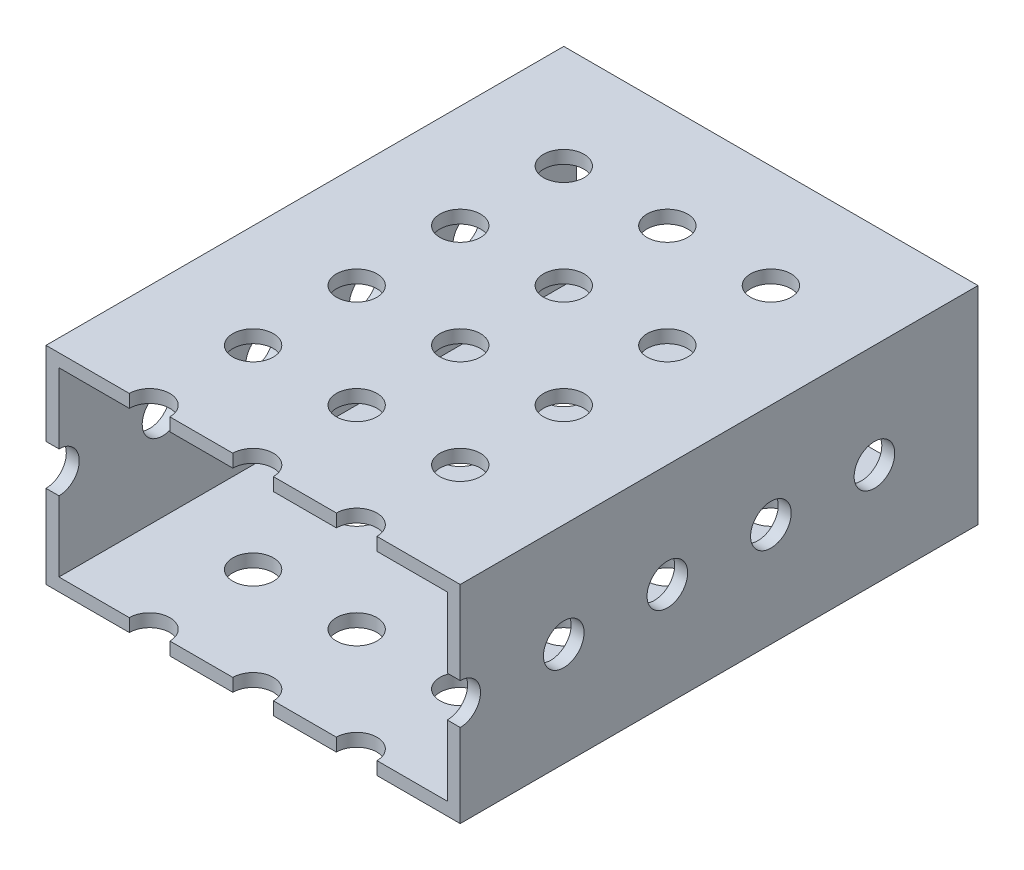
SolidWorks part; units mm, degrees
ref_plane "Front Plane" through (0, 0, 0) normal (0, 0, 1) x (1, 0, 0)
ref_plane "Top Plane" through (0, 0, 0) normal (0, 1, 0) x (1, 0, 0)
ref_plane "Right Plane" through (0, 0, 0) normal (1, 0, 0) x (0, 0, -1)
sketch "Sketch1" plane through (0, 0, 0) normal (0, 0, 1) x (1, 0, 0)
  line L0 (1.5875, 1.5875) -> (49.2125, 1.5875)
  line L1 (0, 0) -> (50.8, 0)
  line L2 (0, 0) -> (0, 25.4)
  line L3 (0, 25.4) -> (50.8, 25.4)
  line L4 (50.8, 0) -> (50.8, 25.4)
  line L5 (49.2125, 1.5875) -> (49.2125, 23.8125)
  line L6 (1.5875, 23.8125) -> (49.2125, 23.8125)
  line L7 (1.5875, 1.5875) -> (1.5875, 23.8125)
  dimension "D1" = 50.8
  dimension "D2" = 25.4
  dimension "D3" = 1.5875
extrude "Boss-Extrude1" add sketch "Sketch1" along normal blind 63.5
sketch "Sketch2" plane through (0, 25.4, 0) normal (0, 1, 0) x (1, 0, 0)
  line L0 (50.8, 0) -> (0, 0) construction
  line L1 (0, -63.5) -> (0, 0) construction
  line L2 (12.7, -12.7) -> (25.4, -12.7) construction
  line L3 (12.7, -12.7) -> (12.7, -25.4) construction
  circle A0 centre (12.7, -12.7) radius 2.4892
  circle A1 centre (25.4, -12.7) radius 2.4892
  circle A2 centre (38.1, -12.7) radius 2.4892
  circle A3 centre (25.4, -25.4) radius 2.4892
  circle A4 centre (38.1, -25.4) radius 2.4892
  circle A5 centre (25.4, -38.1) radius 2.4892
  circle A6 centre (38.1, -38.1) radius 2.4892
  circle A7 centre (25.4, -50.8) radius 2.4892
  circle A8 centre (38.1, -50.8) radius 2.4892
  circle A9 centre (25.4, -63.5) radius 2.4892
  circle A10 centre (38.1, -63.5) radius 2.4892
  circle A11 centre (12.7, -25.4) radius 2.4892
  circle A12 centre (12.7, -38.1) radius 2.4892
  circle A13 centre (12.7, -50.8) radius 2.4892
  circle A14 centre (12.7, -63.5) radius 2.4892
  point P6 (0, 0)
  dimension "D1" = 4.9784
  dimension "D2" = 12.7
  dimension "D3" = 12.7
  dimension "D6" = 90
  dimension "D7" = 12.7
  dimension "D8" = 12.7
  dimension "D4" = 3
  dimension "D5" = 5
extrude "Cut-Extrude1" cut sketch "Sketch2" against normal through all
sketch "Sketch3" plane through (0, 0, 0) normal (-1, 0, 0) x (0, 0, 1)
  line L0 (0, 25.4) -> (0, 0) construction
  line L1 (63.5, 25.4) -> (0, 25.4) construction
  line L2 (12.7, 12.7) -> (25.4, 12.7) construction
  circle A0 centre (12.7, 12.7) radius 2.4892
  circle A1 centre (25.4, 12.7) radius 2.4892
  circle A2 centre (38.1, 12.7) radius 2.4892
  circle A3 centre (50.8, 12.7) radius 2.4892
  circle A4 centre (63.5, 12.7) radius 2.4892
  dimension "D1" = 12.7
  dimension "D3" = 4.9784
  dimension "D2" = 12.7
  dimension "D5" = 12.7
  dimension "D4" = 5
extrude "Cut-Extrude2" cut sketch "Sketch3" against normal through all
